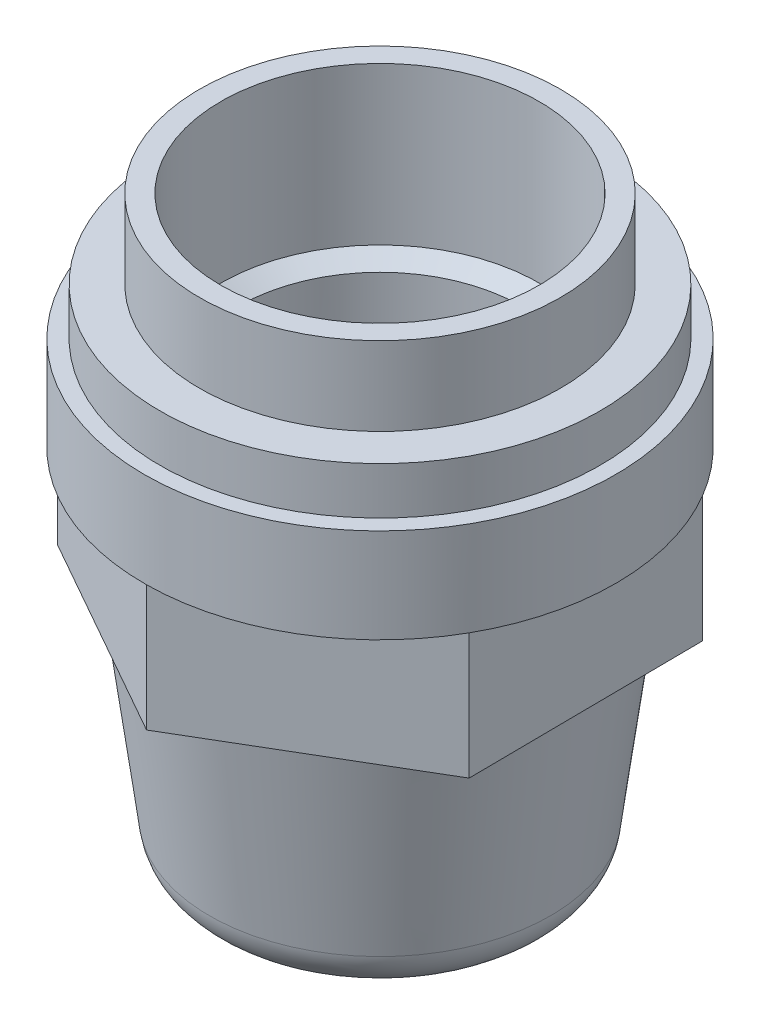
SolidWorks part; units mm, degrees
ref_plane "Спереди" through (0, 0, 0) normal (0, 0, 1) x (1, 0, 0)
ref_plane "Сверху" through (0, 0, 0) normal (0, 1, 0) x (1, 0, 0)
ref_plane "Справа" through (0, 0, 0) normal (1, 0, 0) x (0, 0, -1)
sketch3d "Трехмерный эскиз1"
  line L0 (-7.8685, 0.1302, 0) -> (-4.5, 0.1302, 0)
  line L1 (-10.8429, 2.7366, -0.1171) -> (-12.4716, 15.1151, -0.6732)
  line L2 (-12.4716, 15.1151, -0.6732) -> (-12.4716, 23.1151, -0.6732)
  line L3 (-12.4716, 23.1151, -0.6732) -> (-14.9849, 23.1151, -0.6732)
  line L4 (-14.9849, 23.1151, -0.6732) -> (-14.9849, 29.1151, -0.6732)
  line L5 (-14.9849, 29.1151, -0.6732) -> (-13.9838, 29.1151, -0.6732)
  line L6 (-13.9838, 29.1151, -0.6732) -> (-13.9838, 32.1151, -0.6732)
  line L15 (0, 0, 0) -> (0, 46.3435, 0) construction
  line L16 (-12.4716, 15.1151, -0.6732) -> (6.4801, 15.1151, -0.6732) construction
  line L17 (-10.5, 0.1302, 0) -> (-10.5, 44.3644, 0) construction
  line L18 (-13.9838, 32.1151, -0.6732) -> (-11.4803, 32.1151, -0.6732)
  line L19 (-11.4803, 32.1151, -0.6732) -> (-11.4803, 37.1151, -0.6732)
  line L20 (-11.4803, 37.1151, -0.6732) -> (-8.9748, 37.1151, -0.6732)
  line L21 (-8.9748, 37.1151, -0.6732) -> (-8.9748, 23.1151, -0.6732)
  line L22 (-8.9748, 23.1151, -0.6732) -> (-6.9748, 23.1151, -0.6732)
  line L23 (-6.9748, 23.1151, -0.6732) -> (-6.9748, 18.1151, -0.6732)
  line L24 (-6.9748, 18.1151, -0.6732) -> (-4.4494, 18.1151, -0.6732)
  line L25 (-4.4494, 18.1151, -0.6732) -> (-4.4906, 3.4799, -0.1254)
  line L26 (-4.5, 0.1302, 0) -> (0, 0, 0) construction
  line L27 (-4.4906, 3.4799, -0.1254) -> (-6.4881, 3.4892, -0.0258)
  line L29 (-4.4934, 2.4806, -0.088) -> (-6.4909, 2.4899, 0.0116)
  line L30 (-6.4881, 3.4892, -0.0258) -> (-6.4909, 2.4899, 0.0116)
  line L31 (-4.4906, 3.4799, -0.1254) -> (-6.4909, 2.4899, 0.0116) construction
  line L32 (-4.4934, 2.4806, -0.088) -> (-6.4881, 3.4892, -0.0258) construction
  line L33 (-4.4934, 2.4806, -0.088) -> (-4.5, 0.1302, 0)
  arc A0 (-10.8429, 2.7366, -0.1171) -> (-7.8685, 0.1302, 0) centre (-7.8685, 3.1272, -0.1346) ccw
  point P13 (-10.5, 0.1302, 0)
  point P18 (-5.4907, 2.9849, -0.0569)
  point P23 (-7.8685, 3.2618, 2.8623)
  point P30 (-4.5, 0.1302, 0)
  point P31 (-4.4933, 2.4962, -0.0886)
  point P32 (-6.4363, 3.4394, -0.027)
  point P33 (0, 0, 0)
  point P34 (0, 0, 0)
  point P35 (0, 0, 0)
  point P36 (0, 0, 0)
  point P37 (0, 0, 0)
  point P38 (0, 0, 0)
  dimension "D13" = 3
  dimension "D3" = 4.5
  dimension "D2" = 6
  dimension "D4" = 15
  dimension "D19" = 1
  dimension "D5" = 8
  dimension "D6" = 6
  dimension "D7" = 15
  dimension "D10" = 3
  dimension "D8" = 14
  dimension "D9" = 10.5
  dimension "D11" = 5
  dimension "D12" = 11.5
  dimension "D14" = 9
  dimension "D15" = 14
  dimension "D16" = 2
  dimension "D17" = 5
  dimension "D18" = 4.5
  dimension "D20" = 2
sketch "Эскиз2" plane through (0, 0, 0) normal (0, 0, 1) x (1, 0, 0)
  line L0 (0, 0) -> (0, 46.3435) construction
  line L1 (0, 46.3435) -> (0, 15.1151) construction
  line L2 (0, 0) -> (0, 46.3435) construction
  line L3 (0, 15.1151) -> (6.4801, 15.1151) construction
  line L4 (6.4801, 15.1151) -> (-12.4716, 15.1151) construction
  line L5 (-4.5, 0.1302) -> (-7.8689, 0.1302)
  line L6 (-10.8432, 2.7388) -> (-12.4716, 15.1151)
  line L7 (-12.4716, 15.1151) -> (-12.4716, 23.1151)
  line L8 (-12.4716, 23.1151) -> (-14.9849, 23.1151)
  line L9 (-14.9849, 23.1151) -> (-14.9849, 29.1151)
  line L10 (-14.9849, 29.1151) -> (-13.9838, 29.1151)
  line L11 (-13.9838, 29.1151) -> (-13.9838, 32.1151)
  line L12 (-13.9838, 32.1151) -> (-11.4803, 32.1151)
  line L13 (-11.4803, 32.1151) -> (-11.4803, 37.1151)
  line L14 (-11.4803, 37.1151) -> (-8.9748, 37.1151)
  line L15 (-8.9748, 37.1151) -> (-8.9748, 23.1151)
  line L16 (-8.9748, 23.1151) -> (-6.9748, 23.1151)
  line L17 (-6.9748, 23.1151) -> (-6.9748, 18.1151)
  line L18 (-6.9748, 18.1151) -> (-4.4494, 18.1151)
  line L19 (-4.4494, 18.1151) -> (-4.4906, 3.4799)
  line L20 (-4.4906, 3.4799) -> (-6.4881, 3.4892)
  line L21 (-6.4881, 3.4892) -> (-6.4909, 2.4899)
  line L22 (-6.4909, 2.4899) -> (-4.4934, 2.4806)
  line L23 (-4.4934, 2.4806) -> (-4.5, 0.1302)
  line L24 (-10.5, 0.1302) -> (-10.5, 44.3644) construction
  arc A0 (-7.8689, 0.1302) -> (-10.8432, 2.7388) centre (-7.8689, 3.1302) cw
  point P42 (-10.5, 0.1302)
  point P51 (-10.5, 0.1302)
  dimension "D1" = 3
revolve "Повернуть1" add sketch "Эскиз2" angle 360 about L15
sketch "Эскиз4" plane through (0, 23.1151, 0) normal (0, -1, 0) x (-1, 0, 0)
  line L1 (-13.0449, -7.3741) -> (-0.1363, -14.9843)
  line L2 (-0.1363, -14.9843) -> (12.9086, -7.6102)
  line L3 (12.9086, -7.6102) -> (13.0449, 7.3741)
  line L4 (13.0449, 7.3741) -> (0.1363, 14.9843)
  line L5 (0.1363, 14.9843) -> (-12.9086, 7.6102)
  line L6 (-12.9086, 7.6102) -> (-13.0449, -7.3741)
  circle A0 centre (0, 0) radius 12.9773 construction
  circle A1 centre (0, 0) radius 12.4716
extrude "Бобышка-Вытянуть2" add sketch "Эскиз4" along normal blind 8
sketch "Эскиз6" plane through (0, 37.1151, 0) normal (0, 1, 0) x (1, 0, 0)
  circle A1 centre (0, 0) radius 8.9748
  point P0 (0, 0)
extrude "Бобышка-Вытянуть3" add sketch "Эскиз6" against normal blind 8
hole_wizard "Сверло под метчик  спиральное M201" positions "Эскиз7" profile "Эскиз8" hole size "M20x1.5" standard "DIN"
sketch "Эскиз7" plane through (0, 37.1151, 0) normal (0, 1, 0) x (1, 0, 0)
  point P0 (0, 0)
sketch "Эскиз8" plane through (0, 37.1151, 0) normal (1, 0, 0) x (0, 0, 1)
  line L0 (0, 0) -> (0, 16.0837)
  line L1 (0, 16.0837) -> (10.125, 10)
  line L2 (10.125, 10) -> (10.125, 0)
  line L5 (10.125, 0) -> (0, 0)
  line L10 (0, 16.0837) -> (-10.125, 10) construction
  line L11 (0, -6.35) -> (0, 107.95) construction
  dimension "Диаметр отверстия" = 20.25
  dimension "Глубина отверстия" = 10
  dimension "Угол заточки сверла" = 118
